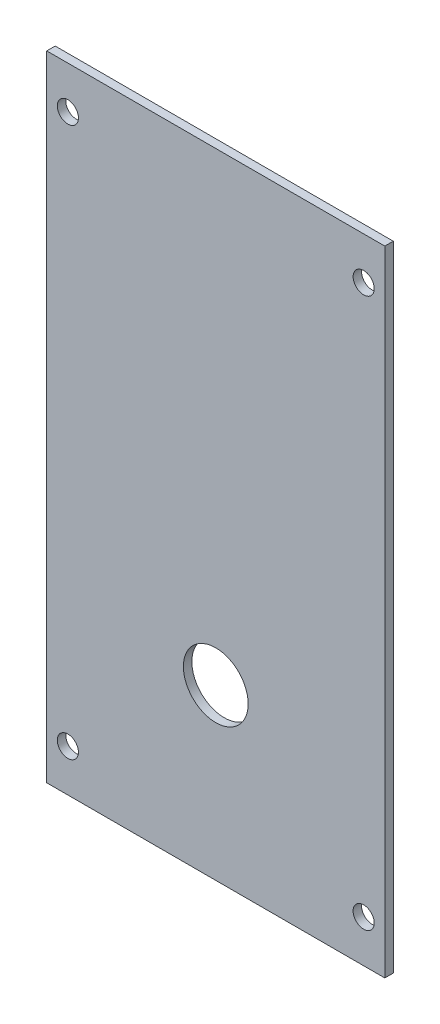
SolidWorks part; units mm, degrees
ref_plane "Front Plane" through (0, 0, 0) normal (0, 0, 1) x (1, 0, 0)
ref_plane "Top Plane" through (0, 0, 0) normal (0, 1, 0) x (1, 0, 0)
ref_plane "Right Plane" through (0, 0, 0) normal (1, 0, 0) x (0, 0, -1)
sketch "Sketch1" plane through (0, 0, 0) normal (0, 0, 1) x (1, 0, 0)
  line L1 (-18.0488, 49.439) -> (21.9512, 49.439)
  line L2 (-18.0488, 49.439) -> (-18.0488, -25.561)
  line L3 (-18.0488, -25.561) -> (21.9512, -25.561)
  line L4 (21.9512, 49.439) -> (21.9512, -25.561)
  circle A0 centre (-15.5488, 44.439) radius 1.25
  circle A1 centre (19.4512, 44.439) radius 1.25
  circle A2 centre (19.4512, -20.561) radius 1.25
  circle A3 centre (-15.5488, -20.561) radius 1.25
  dimension "D3" = 2.5
  dimension "D5" = 2.5
  dimension "D6" = 2.5
  dimension "D8" = 2.5
  dimension "D9" = 2.5
  dimension "D1" = 40
  dimension "D2" = 75
  dimension "D4" = 2.5
  dimension "D7" = 2.5
  dimension "D10" = 2.5
  dimension "D11" = 5
  dimension "D12" = 5
  dimension "D13" = 5
  dimension "D14" = 5
  dimension "D15" = 2.5
extrude "Boss-Extrude1" add sketch "Sketch1" along normal blind 1
sketch "Sketch2" plane through (0, 0, 1) normal (0, 0, 1) x (1, 0, 0)
  line L1 (-18.0488, -25.561) -> (21.9512, -25.561) construction
  line L2 (21.9512, -25.561) -> (21.9512, 49.439) construction
  circle A0 centre (1.9512, -5.561) radius 3.832
  point P6 (30.5059, 1.0835)
  dimension "D1" = 20
  dimension "D2" = 20
extrude "Cut-Extrude1" cut sketch "Sketch2" against normal blind 10
